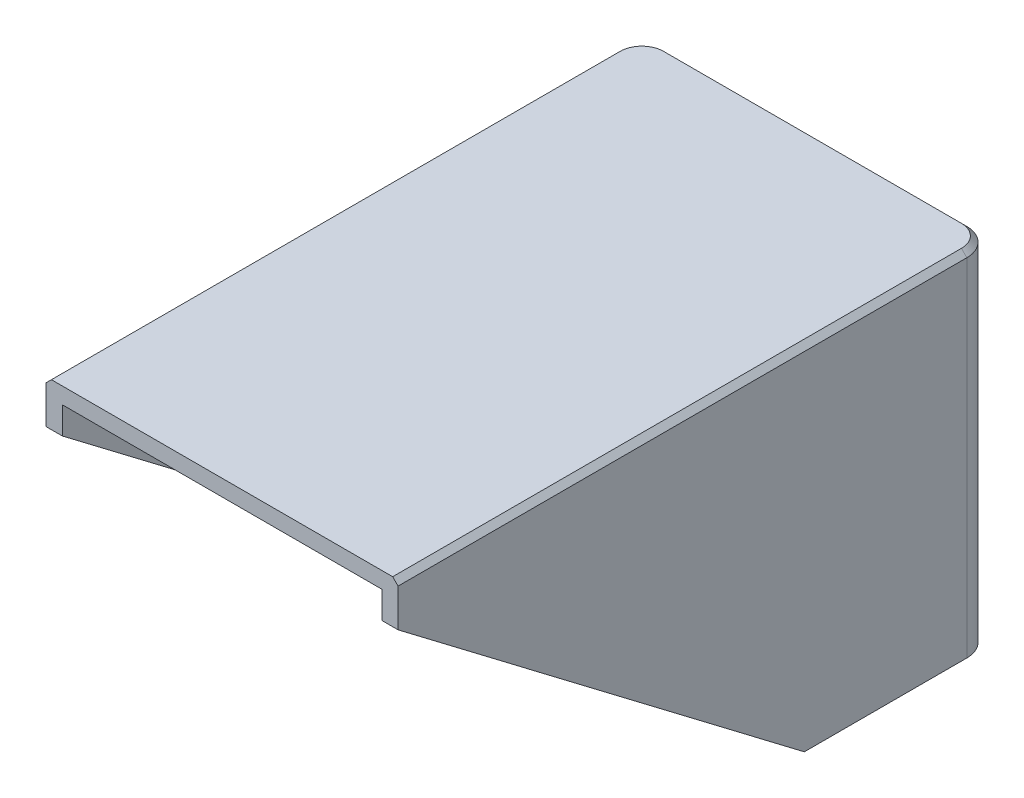
SolidWorks part; units mm, degrees
ref_plane "Plan de face" through (0, 0, 0) normal (0, 0, 1) x (1, 0, 0)
ref_plane "Plan de dessus" through (0, 0, 0) normal (0, 1, 0) x (1, 0, 0)
ref_plane "Plan de droite" through (0, 0, 0) normal (1, 0, 0) x (0, 0, -1)
sketch "Esquisse1" plane through (0, 0, 0) normal (0, 1, 0) x (1, 0, 0)
  line L1 (-32.5, -62.5) -> (32.5, -62.5)
  line L2 (-32.5, -62.5) -> (-32.5, 62.5)
  line L3 (-32.5, 62.5) -> (32.5, 62.5)
  line L4 (32.5, -62.5) -> (32.5, 62.5)
  line L5 (-32.5, -62.5) -> (32.5, 62.5) construction
  line L6 (-32.5, 62.5) -> (32.5, -62.5) construction
  point P0 (0, 0)
  dimension "D1" = 125
  dimension "D2" = 65
extrude "Boss.-Extru.1" add sketch "Esquisse1" along normal blind 80
shell "Coque1" thickness 3
sketch "Esquisse2" plane through (32.5, 0, 0) normal (1, 0, 0) x (0, 0, -1)
  line L0 (-47.5, 80) -> (-47.5, 72)
  line L1 (-62.5, 80) -> (62.5, 80) construction
  line L2 (-47.5, 72) -> (27.5, 15)
  line L3 (27.5, 15) -> (62.5, 15)
  line L4 (62.5, 80) -> (62.5, 0) construction
  line L5 (62.5, 15) -> (62.5, 80)
  line L6 (62.5, 80) -> (-47.5, 80)
  line L7 (-62.5, 80) -> (-62.5, 0) construction
  line L8 (-62.5, 0) -> (62.5, 0) construction
  dimension "D1" = 15
  dimension "D2" = 15
  dimension "D3" = 35
  dimension "D4" = 8
extrude "Enlèv. mat.-Extru.1" cut sketch "Esquisse2" against normal through all flip side to cut
fillet "Congé2" radius 5 2 edges at (-32.5, 47.5, -62.5) (32.5, 47.5, -62.5)
fillet "Congé3" radius 2 2 edges at (29.5, 46, -59.5) (-29.5, 46, -59.5)
chamfer "Chanfrein1" distance 1 angle 45 5 edges at (-32.5, 80, -5) (-31.0355, 80, -61.0355) (32.5, 80, -5) (0, 80, -62.5) (31.0355, 80, -61.0355)
sketch "Esquisse3" plane through (0, 0, -62.5) normal (0, 0, -1) x (-1, 0, 0)
  line L0 (27.5, 15) -> (-27.5, 15) construction
  line L1 (31.5, 80) -> (-31.5, 80) construction
  circle A0 centre (0, 55) radius 15.24
  point P2 (0, 0)
  point P5 (0, 15)
  dimension "D1" = 30.48
  dimension "D2" = 25
extrude "Enlèv. mat.-Extru.2" cut sketch "Esquisse3" against normal blind 0.1
